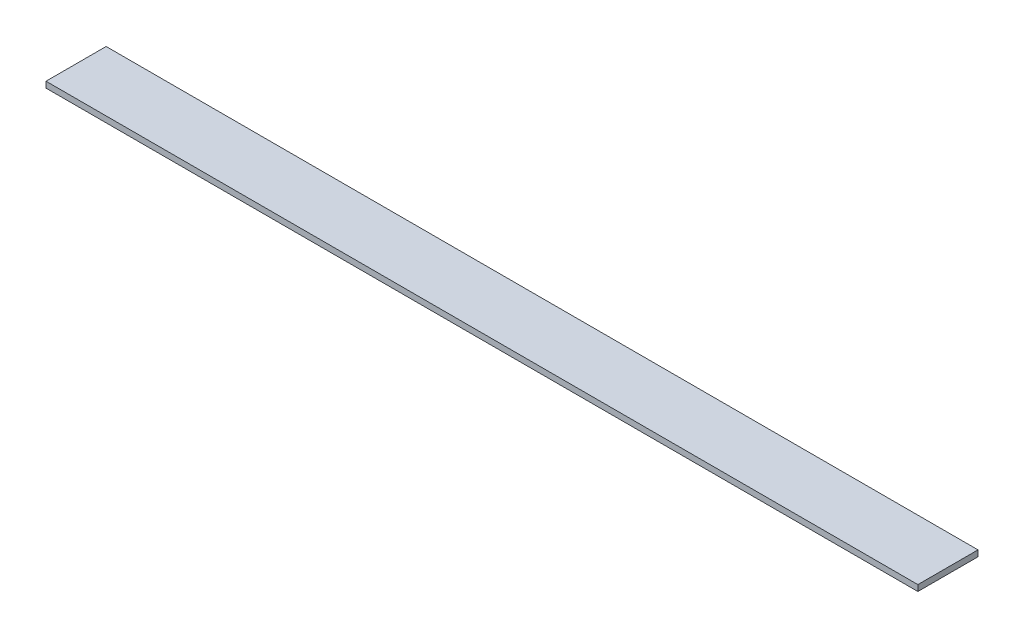
SolidWorks part; units mm, degrees
ref_plane "Face" through (0, 0, 0) normal (0, 0, 1) x (1, 0, 0)
ref_plane "Dessus" through (0, 0, 0) normal (0, 1, 0) x (1, 0, 0)
ref_plane "Droite" through (0, 0, 0) normal (1, 0, 0) x (0, 0, -1)
sketch "Esquisse1" plane through (0, 0, 0) normal (0, 1, 0) x (1, 0, 0)
  line L1 (0, 0) -> (1450, 0)
  line L2 (0, 0) -> (0, 100)
  line L3 (0, 100) -> (1450, 100)
  line L4 (1450, 0) -> (1450, 100)
  dimension "D1" = 1450
  dimension "D2" = 100
extrude "Extrusion1" add sketch "Esquisse1" along normal blind 10
